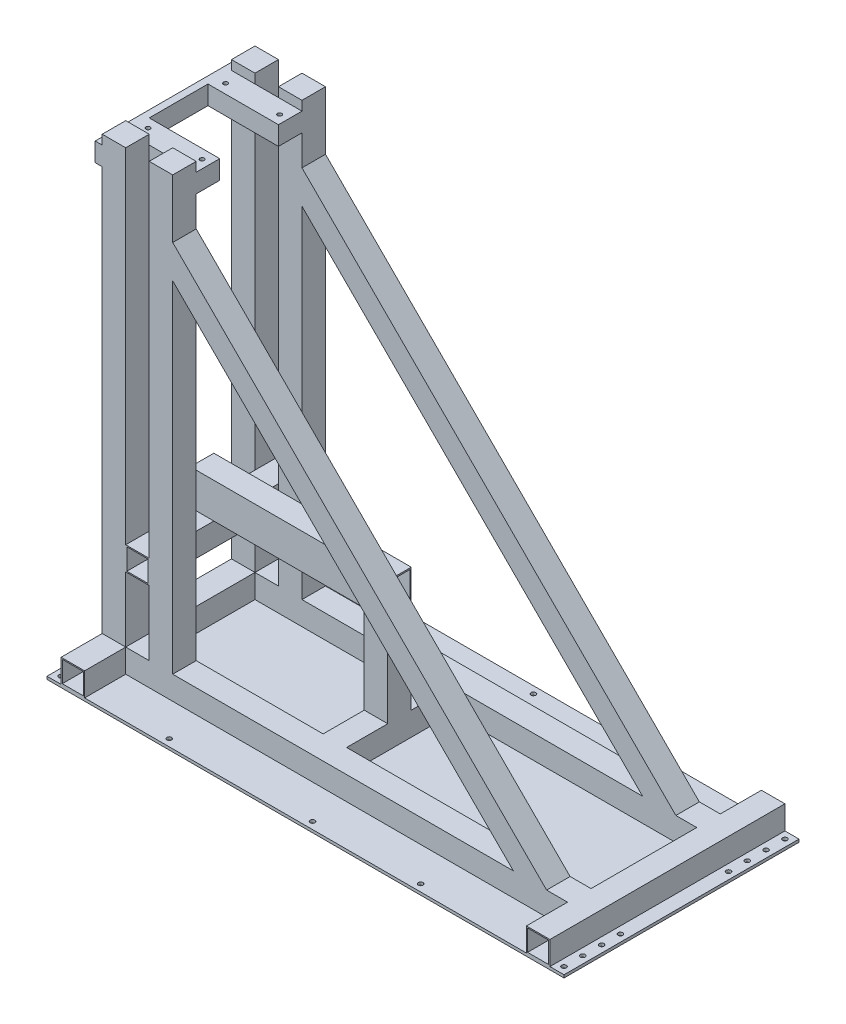
SolidWorks part; units mm, degrees
material "Plain Carbon Steel"
ref_plane "Front Plane" through (0, 0, 0) normal (0, 0, 1) x (1, 0, 0)
ref_plane "Top Plane" through (0, 0, 0) normal (0, 1, 0) x (1, 0, 0)
ref_plane "Right Plane" through (0, 0, 0) normal (1, 0, 0) x (0, 0, -1)
sketch "Base" plane through (0, 0, 0) normal (0, 0, 1) x (1, 0, 0)
  line L1 (0, 100) -> (0, 1940)
  line L2 (100, 1549.5689) -> (100, 100)
  line L3 (100, 0) -> (0, 0)
  line L4 (100, 0) -> (1880, 0)
  line L5 (1690.9903, 100) -> (1880, 100)
  line L6 (1549.5689, 100) -> (100, 100)
  line L7 (100, 1690.9903) -> (1690.9903, 100)
  line L8 (100, 1549.5689) -> (1549.5689, 100)
  line L9 (50, 1940) -> (50, 0) construction
  line L10 (1880, 50) -> (50, 50) construction
  line L11 (1880, 100) -> (1880, 0)
  line L12 (100, 1690.9903) -> (100, 1940)
  line L13 (100, 1940) -> (0, 1940)
  line L15 (-100, 1940) -> (-200, 1940)
  line L16 (-200, 1940) -> (-200, 0)
  line L17 (-200, 0) -> (-100, 0)
  line L19 (-100, 0) -> (0, 0)
  line L21 (-100, 1940) -> (-100, 100)
  line L22 (-100, 100) -> (0, 100)
  circle A0 centre (50, 1183) radius 25 construction
  dimension "D7" = 50
  dimension "D1" = 1940
  dimension "D2" = 1780
  dimension "D3" = 100
  dimension "D4" = 100
  dimension "D5" = 100
  dimension "D6" = 100
  dimension "D8" = 2250
  dimension "D9" = 45
  dimension "D10" = 100
  dimension "D11" = 100
  dimension "D12" = 100
extrude "Boss-Extrude1" add sketch "Base" along normal blind 100
sketch "Sketch15" plane through (0, 0, 0) normal (0, 0, 1) x (1, 0, 0)
  line L0 (100, 1687.4547) -> (100, 1556.64)
  line L1 (-197.5, 1937.5) -> (-102.5, 1937.5)
  line L2 (-197.5, 1937.5) -> (-197.5, 100)
  line L3 (-197.5, 100) -> (-102.5, 100)
  line L4 (-102.5, 1937.5) -> (-102.5, 100)
  line L5 (2.5, 1937.5) -> (97.5, 1937.5)
  line L6 (2.5, 1937.5) -> (2.5, 100)
  line L7 (2.5, 100) -> (97.5, 100)
  line L8 (97.5, 1937.5) -> (97.5, 100)
  line L9 (-200, 2.5) -> (1880, 2.5)
  line L10 (-200, 2.5) -> (-200, 97.5)
  line L11 (-200, 0) -> (1880, 0)
  line L12 (1880, 0) -> (1880, 100)
  line L13 (1880, 100) -> (1690.9903, 100)
  line L14 (1690.9903, 100) -> (100, 1690.9903)
  line L15 (100, 1690.9903) -> (100, 1940)
  line L16 (100, 1940) -> (0, 1940)
  line L17 (0, 1940) -> (0, 100)
  line L18 (0, 100) -> (-100, 100)
  line L19 (-100, 100) -> (-100, 1940)
  line L20 (-100, 1940) -> (-200, 1940)
  line L21 (-200, 1940) -> (-200, 0)
  line L22 (-200, 0) -> (1880, 0) construction
  line L23 (1880, 0) -> (1880, 100) construction
  line L24 (1880, 100) -> (1690.9903, 100) construction
  line L25 (1690.9903, 100) -> (100, 1690.9903) construction
  line L26 (100, 1690.9903) -> (100, 1940) construction
  line L27 (100, 1940) -> (0, 1940) construction
  line L28 (0, 1940) -> (0, 100) construction
  line L29 (0, 100) -> (-100, 100) construction
  line L30 (-100, 100) -> (-100, 1940) construction
  line L31 (-100, 1940) -> (-200, 1940) construction
  line L32 (-200, 1940) -> (-200, 0) construction
  line L33 (-200, 97.5) -> (1880, 97.5)
  line L34 (1880, 2.5) -> (1880, 97.5)
  line L35 (100, 1556.64) -> (1556.64, 100)
  line L36 (1556.64, 100) -> (1687.4547, 100)
  line L37 (1687.4547, 100) -> (100, 1687.4547)
  line L38 (1549.5689, 100) -> (100, 1549.5689) construction
  dimension "D2" = 5
  dimension "D3" = 5
  dimension "D4" = 5
  dimension "D5" = 5
  dimension "D6" = 5
  dimension "D7" = 5
  dimension "D8" = 5
  dimension "D9" = 5
  dimension "D10" = 5
  dimension "D11" = 5
  dimension "D1" = 0
extrude "Cut-Extrude3" cut sketch "Sketch15" along normal blind 90 from offset 5
sketch "Sketch1" plane through (0, 0, 0) normal (0, 0, -1) x (-1, 0, 0)
  line L2 (-100, 1549.5689) -> (-100, 100) construction
  line L3 (-100, 1900) -> (10.4196, 1900)
  line L4 (-100, 1900) -> (-100, 1820)
  line L6 (-100, 1820) -> (200, 1820)
  line L8 (200, 1900) -> (200, 1820)
  line L9 (200, 1940) -> (200, 0) construction
  line L10 (50, 1820) -> (50, 1760.7228) construction
  line L11 (10.4196, 1900) -> (200, 1900)
  dimension "D1" = 80
  dimension "D2" = 1900
extrude "Boss-Extrude2" add sketch "Sketch1" along normal blind 100
sketch "Sketch3" plane through (0, 0, 0) normal (0, 0, -1) x (-1, 0, 0)
  line L0 (-100, 1900) -> (-100, 1820) construction
  line L1 (200, 1900) -> (-100, 1900) construction
  line L2 (-73.2624, 1900) -> (163.5519, 1900) construction
  line L3 (0, 1900) -> (-100, 1900) construction
  line L4 (-100, 1900) -> (-100, 1820) construction
  line L5 (-100, 1860) -> (180.1024, 1860) construction
  line L6 (50, 2133.9205) -> (50, 1775.6528) construction
  line L7 (200, 1900) -> (100, 1900) construction
  line L8 (-73.2624, 1900) -> (-73.2624, 1940) construction
  line L9 (163.5519, 1780) -> (163.5519, 1820)
  line L10 (-73.2624, 1940) -> (-10, 1940) construction
  line L11 (110, 1940) -> (163.5519, 1940) construction
  line L12 (163.5519, 1940) -> (163.5519, 1900) construction
  line L13 (110, 1780) -> (163.5519, 1780)
  line L14 (-73.2624, 1780) -> (-10, 1780)
  line L15 (-73.2624, 1820) -> (-73.2624, 1780)
  line L16 (-73.2624, 1820) -> (163.5519, 1820)
  arc A0 (-10, 1940) -> (110, 1940) centre (50, 1940) cw construction
  circle A1 centre (50, 1940) radius 30 construction
  circle A2 centre (50, 1780) radius 30
  arc A3 (-10, 1780) -> (110, 1780) centre (50, 1780) ccw
  point P2 (50, 1900)
  dimension "D3" = 40
  dimension "D1" = 60
  dimension "D2" = 60
sketch "Sketch2" plane through (0, 1900, 0) normal (0, 1, 0) x (1, 0, 0)
  line L0 (-180, 60) -> (65, 60) construction
  line L3 (-50, 100) -> (-50, 0) construction
  line L4 (-200, 100) -> (100, 100) construction
  line L5 (-100, 0) -> (0, 0) construction
  circle A0 centre (-165, 60) radius 9
  circle A1 centre (65, 60) radius 9
  dimension "D1" = 18
  dimension "D2" = 18
  dimension "D3" = 115
  dimension "D4" = 115
  dimension "D5" = 40
extrude "Cut-Extrude1" cut sketch "Sketch2" against normal through all and the other way through all
ref_plane "Plane1" through (0, 0, -225) normal (0, 0, 1) x (1, 0, 0)
mirror "Mirror2" about plane through (0, 0, -225) normal (0, 0, 1) of bodies 104 101 106 114 116
sketch "Sketch5" plane through (0, 0, -225) normal (0, 0, 1) x (1, 0, 0)
  line L0 (-200, 0) -> (1880, 0) construction
  line L1 (-200, 1820) -> (-200, 0) construction
  line L2 (1880, 0) -> (1880, 100) construction
  line L3 (-200, 0) -> (1880, 0) construction
  line L4 (-200, 1820) -> (-200, 0) construction
  line L5 (1880, 0) -> (1880, 100) construction
  line L6 (-150, 95) -> (-150, 100) construction
  line L7 (-200, 0) -> (-100, 0)
  line L8 (-200, 0) -> (-200, 100)
  line L9 (-200, 100) -> (-100, 100)
  line L10 (-100, 0) -> (-100, 100)
  line L11 (1880, 0) -> (1780, 0)
  line L12 (1880, 0) -> (1880, 100)
  line L13 (1880, 100) -> (1780, 100)
  line L14 (1780, 0) -> (1780, 100)
  line L15 (-195, 95) -> (-105, 95)
  line L16 (-195, 95) -> (-195, 5)
  line L17 (-195, 5) -> (-105, 5)
  line L18 (-105, 95) -> (-105, 5)
  line L19 (-105, 50) -> (-100, 50) construction
  line L20 (1830, 95) -> (1830, 100) construction
  line L21 (1785, 95) -> (1875, 95)
  line L22 (1785, 95) -> (1785, 5)
  line L23 (1785, 5) -> (1875, 5)
  line L24 (1875, 95) -> (1875, 5)
  line L25 (1785, 50) -> (1780, 50) construction
  dimension "D1" = 100
  dimension "D2" = 100
  dimension "D3" = 100
  dimension "D4" = 5
  dimension "D5" = 5
extrude "Boss-Extrude6" add sketch "Sketch5" along normal blind 500 and the other way blind 500
sketch "Sketch6" plane through (-200, 0, 0) normal (-1, 0, 0) x (0, 0, 1)
  line L0 (-550, 1940) -> (-550, 100) construction
  line L1 (-550, 1820) -> (100, 1820)
  line L2 (-550, 1820) -> (-550, 1900)
  line L3 (-550, 1900) -> (100, 1900)
  line L4 (100, 1820) -> (100, 1900)
  line L5 (100, 1940) -> (100, 100) construction
  line L6 (-350, 1820) -> (-450, 1820) construction
  line L7 (-350, 1900) -> (-450, 1900) construction
extrude "Boss-Extrude7" add sketch "Sketch6" along normal blind 30
sketch "Sketch7" plane through (0, 0, 0) normal (-1, 0, 0) x (0, 0, 1)
  line L0 (100, 1940) -> (100, 100) construction
  line L1 (100, 477) -> (-550, 477)
  line L2 (100, 477) -> (100, 377)
  line L3 (100, 377) -> (-550, 377)
  line L4 (-550, 477) -> (-550, 377)
  line L5 (-550, 1940) -> (-550, 100) construction
  dimension "D1" = 100
  dimension "D2" = 477
extrude "Boss-Extrude8" add sketch "Sketch7" along normal blind 100
sketch "Sketch8" plane through (0, 0, -225) normal (0, 0, 1) x (1, 0, 0)
  line L0 (-100, 477) -> (0, 477) construction
  line L1 (-100, 477) -> (-100, 1940) construction
  line L2 (0, 377) -> (0, 100) construction
  line L3 (-100, 377) -> (0, 377) construction
  line L4 (-100, 477) -> (0, 477) construction
  line L5 (-100, 477) -> (-100, 1940) construction
  line L6 (0, 377) -> (0, 100) construction
  line L7 (-100, 377) -> (0, 377) construction
  line L8 (-100, 377) -> (-100, 477) construction
  line L9 (0, 477) -> (0, 377) construction
  line L10 (-95, 472) -> (-5, 472)
  line L11 (-5, 472) -> (-5, 382)
  line L12 (-95, 382) -> (-5, 382)
  line L13 (-95, 382) -> (-95, 472)
  dimension "D1" = 5
extrude "Cut-Extrude2" cut sketch "Sketch8" against normal mid plane 760
sketch "Sketch9" plane through (0, 0, -225) normal (0, 0, 1) x (1, 0, 0)
  line L0 (1549.5689, 100) -> (100, 1549.5689) construction
  line L1 (1690.9903, 100) -> (100, 1690.9903) construction
  line L2 (1549.5689, 100) -> (100, 1549.5689) construction
  line L3 (1690.9903, 100) -> (100, 1690.9903) construction
  line L4 (1172.5689, 477) -> (1130.1425, 477)
  line L5 (1172.5689, 477) -> (1207.9242, 441.6447)
  line L6 (1207.9242, 441.6447) -> (1186.711, 420.4315)
  line L7 (1186.711, 420.4315) -> (1130.1425, 477)
  line L8 (1313.9903, 477) -> (1370.5588, 420.4315)
  line L9 (1370.5588, 420.4315) -> (1391.772, 441.6447)
  line L10 (1391.772, 441.6447) -> (1356.4167, 477)
  line L11 (1356.4167, 477) -> (1313.9903, 477)
  line L12 (-100, 477) -> (0, 477) construction
  dimension "D1" = 30
  dimension "D2" = 80
  dimension "D3" = 30
  dimension "D4" = 80
extrude "Boss-Extrude9" [suppressed] add sketch "Sketch9" along normal mid plane 490
sketch "Sketch11" plane through (0, 0, 0) normal (0, 1, 0) x (1, 0, 0)
  line L0 (-1067, 225) -> (1067, 225) construction
  line L1 (-200, -187.5) -> (-260, -187.5) construction
  line L2 (-200, -100) -> (-200, -275) construction
  line L3 (1880, -275) -> (1940, -275) construction
  line B0 (-260, -275) -> (1940, -275)
  line B1 (-260, -275) -> (-260, 725)
  line B2 (1940, -275) -> (1940, 725)
  line B3 (-260, 725) -> (1940, 725)
  line B4 (-260, -275) -> (1940, 725) construction
  line B5 (1940, -275) -> (-260, 725) construction
  line B6 (-187.6178, 637.5) -> (-260, 637.5) construction
  line B7 (1867.6178, 637.5) -> (1940, 637.5) construction
  line B8 (439.3817, 375) -> (439.3817, 455) construction
  line B9 (480.4645, 455) -> (480.4645, 535) construction
  line B10 (527.2532, 535) -> (527.2532, 615) construction
  line B11 (-230, 695) -> (-230, 225) construction
  line B12 (439.3817, 695) -> (439.3817, 615) construction
  line B13 (-344.3667, 225) -> (1910, 225) construction
  line B14 (-230, 695) -> (1910, 695) construction
  line B15 (1910, 695) -> (1910, 225) construction
  line B16 (-230, 455) -> (1910, 455) construction
  line B17 (1910, 535) -> (-230, 535) construction
  line B18 (-230, 615) -> (1910, 615) construction
  circle B19 centre (-230, 695) radius 10
  circle B20 centre (1910, 695) radius 10
  circle B21 centre (1910, 455) radius 10
  circle B22 centre (1910, 535) radius 10
  circle B23 centre (1910, 615) radius 10
  circle B24 centre (1300, 695) radius 10
  circle B25 centre (840, 695) radius 10
  circle B26 centre (230, 695) radius 10
  circle B27 centre (-230, 615) radius 10
  circle B28 centre (-230, 455) radius 10
  circle B29 centre (-230, 535) radius 10
  circle B30 centre (1910, -5) radius 10
  circle B31 centre (1910, -85) radius 10
  circle B32 centre (1910, -165) radius 10
  circle B33 centre (1910, -245) radius 10
  circle B34 centre (1300, -245) radius 10
  circle B35 centre (840, -245) radius 10
  circle B36 centre (230, -245) radius 10
  circle B37 centre (-230, -245) radius 10
  circle B38 centre (-230, -165) radius 10
  circle B39 centre (-230, -85) radius 10
  circle B40 centre (-230, -5) radius 10
sketch_block_instance "Block2-1"
sketch_block "Block2" parameters "D6"=20, "D1"=2200, "D2"=1000, "D3"=30, "D4"=30, "D5"=30, "D7"=460, "D8"=610, "D9"=460
extrude "Boss-Extrude10" add sketch "Sketch11" against normal blind 12
sketch "Sketch12" plane through (-100, 0, 0) normal (-1, 0, 0) x (0, 0, 1)
  line L1 (-225, -1067) -> (-225, 1067) construction
  line L2 (0, 477) -> (-450, 477) construction
  line B0 (-275, 477) -> (-175, 477)
  line B1 (-275, 477) -> (-275, 627)
  line B2 (-175, 477) -> (-175, 627)
  line B3 (-275, 627) -> (-175, 627)
  line B4 (-269, 483) -> (-181, 483)
  line B5 (-269, 483) -> (-269, 621)
  line B6 (-181, 483) -> (-181, 621)
  line B7 (-269, 621) -> (-181, 621)
sketch_block_instance "15x10x6_profil-1"
sketch_block "15x10x6_profil" parameters "D1"=100, "D2"=150, "D3"=6, "D4"=6
extrude "Boss-Extrude11" add sketch "Sketch12" against normal blind 840
sketch "Sketch18" plane through (0, 0, -225) normal (0, 0, 1) x (1, 0, 0)
  line L0 (-100, 0) -> (1780, 0) construction
  line L1 (-100, 0) -> (1780, 0) construction
  line L3 (740, 727) -> (740, 627) construction
  line L4 (740, 477) -> (740, 627) construction
  line B0 (640, 0) -> (740, 0)
  line B1 (640, 0) -> (640, 100)
  line B2 (740, 0) -> (740, 100)
  line B3 (640, 100) -> (740, 100)
  line B4 (645, 5) -> (735, 5)
  line B5 (645, 5) -> (645, 95)
  line B6 (735, 5) -> (735, 95)
  line B7 (645, 95) -> (735, 95)
sketch_block_instance "Block1-2"
sketch_block "Block1" parameters "D1"=100, "D2"=100, "D3"=5, "D4"=5
extrude "Boss-Extrude13" add sketch "Sketch18" along normal mid plane 450
sketch "Sketch14" plane through (0, 477, 0) normal (0, -1, 0) x (1, 0, 0)
  line L1 (740, -175) -> (640, -175)
  line L2 (740, -175) -> (740, -275)
  line L3 (740, -275) -> (640, -275)
  line L4 (640, -175) -> (640, -275)
  line L5 (735, -180) -> (645, -180)
  line L6 (645, -180) -> (645, -270)
  line L7 (735, -270) -> (645, -270)
  line L8 (735, -180) -> (735, -270)
  line L9 (740, -275) -> (0, -275) construction
  dimension "D1" = 100
  dimension "D2" = 5
extrude "Boss-Extrude12" add sketch "Sketch14" along normal up to surface (377 mm away) up to face at (779.8563, 100, -225)
sketch "Sketch16" plane through (0, 0, 100) normal (0, 0, 1) x (1, 0, 0)
  line L4 (-195, 95) -> (-195, 5)
  line L5 (-195, 95) -> (-195, 5)
  line L6 (-195, 5) -> (-105, 5)
  line L7 (-195, 5) -> (-105, 5)
  line L8 (-105, 5) -> (-105, 95)
  line L9 (-105, 5) -> (-105, 95)
  line L10 (-105, 95) -> (-195, 95)
  line L11 (-105, 95) -> (-195, 95)
  dimension "D1" = 0
extrude "Cut-Extrude4" cut sketch "Sketch16" against normal through all
sketch "Sketch17" plane through (0, 0, 100) normal (0, 0, 1) x (1, 0, 0)
  line L4 (1785, 95) -> (1785, 5)
  line L5 (1785, 95) -> (1785, 5)
  line L6 (1785, 5) -> (1875, 5)
  line L7 (1785, 5) -> (1875, 5)
  line L8 (1875, 5) -> (1875, 95)
  line L9 (1875, 5) -> (1875, 95)
  line L10 (1875, 95) -> (1785, 95)
  line L11 (1875, 95) -> (1785, 95)
  dimension "D1" = 0
extrude "Cut-Extrude5" cut sketch "Sketch17" against normal through all
equation "\"D3\"=100"
equation "\"D1\"=20"
